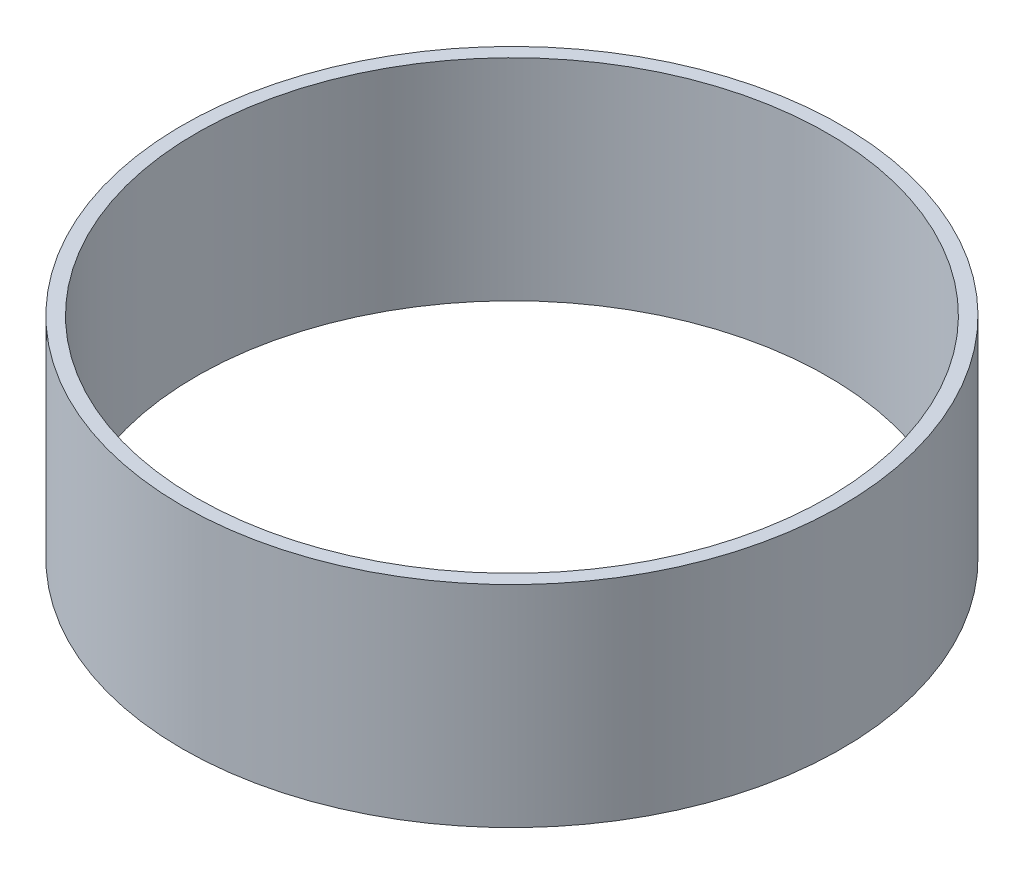
SolidWorks part; units mm, degrees
material "E-Glass Fiber"
ref_plane "Front Plane" through (0, 0, 0) normal (0, 0, 1) x (1, 0, 0)
ref_plane "Top Plane" through (0, 0, 0) normal (0, 1, 0) x (1, 0, 0)
ref_plane "Right Plane" through (0, 0, 0) normal (1, 0, 0) x (0, 0, -1)
sketch "Sketch1" plane through (0, 0, 0) normal (0, 1, 0) x (1, 0, 0)
  circle A0 centre (0, 0) radius 75.565
  circle A1 centre (0, 0) radius 72.39
  dimension "D1" = 151.13
  dimension "D2" = 3.175
extrude "Boss-Extrude1" add sketch "Sketch1" along normal blind 48.26
